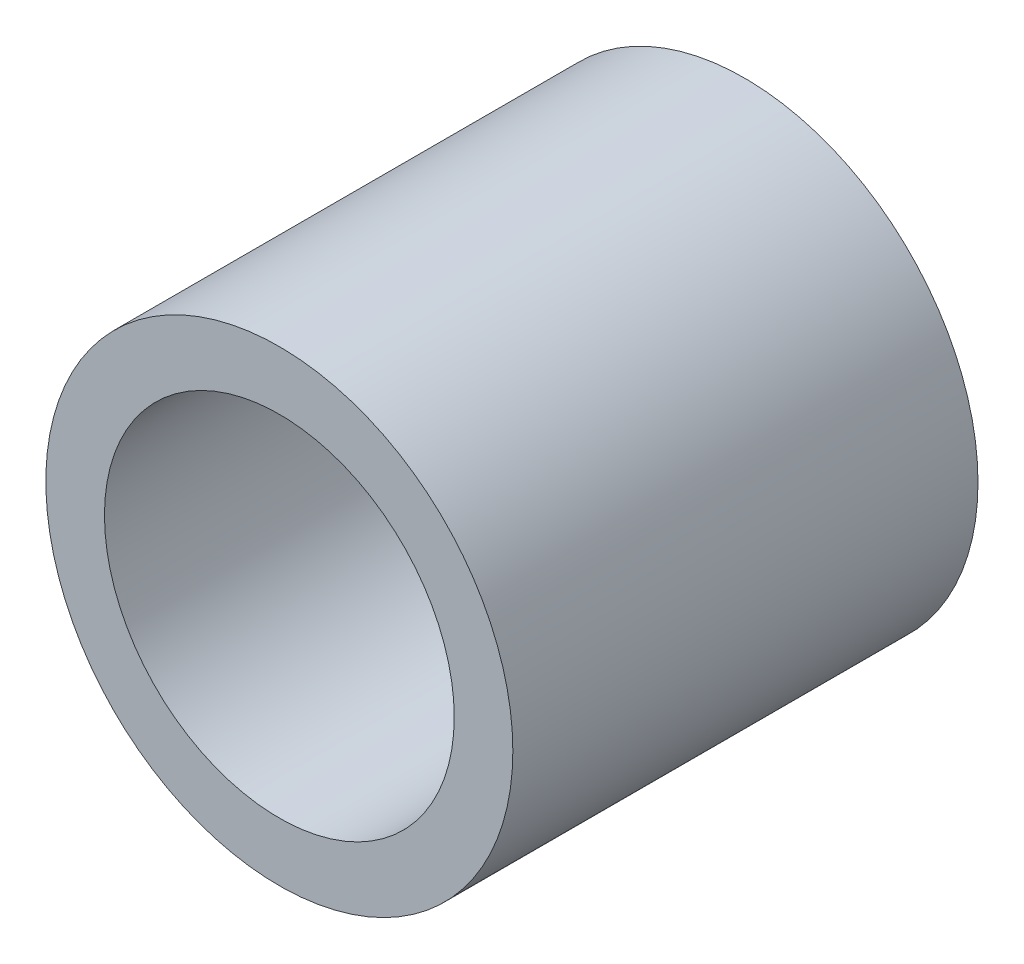
SolidWorks part; units mm, degrees
ref_plane "Front Plane" through (0, 0, 0) normal (0, 0, 1) x (1, 0, 0)
ref_plane "Top Plane" through (0, 0, 0) normal (0, 1, 0) x (1, 0, 0)
ref_plane "Right Plane" through (0, 0, 0) normal (1, 0, 0) x (0, 0, -1)
sketch "Sketch1" plane through (0, 0, 0) normal (0, 0, 1) x (1, 0, 0)
  circle A0 centre (0, 0) radius 6.3754
  circle A1 centre (0, 0) radius 4.7752
  dimension "D1" = 12.7508
  dimension "ID" = 9.5504
extrude "Extrude1" add sketch "Sketch1" along normal mid plane 12.7
sketch "Sketch2" plane through (0, 0, 0) normal (1, 0, 0) x (0, 0, -1)
  line L0 (-6.35, -4.7752) -> (6.35, -4.7752) construction
  line L3 (6.35, 4.7752) -> (-6.35, 4.7752) construction
  line L5 (-6.35, -4.7752) -> (6.35, -4.7752)
  line L6 (6.35, 4.7752) -> (-6.35, 4.7752)
sketch "Sketch4" plane through (0, 0, 6.35) normal (0, 0, 1) x (1, 0, 0)
  line L0 (0, 0) -> (-3.3766, 3.3766)
  line L1 (0, -3.4925) -> (0, 3.4925) construction
  circle A0 centre (0, 0) radius 4.7752 construction
  dimension "D1" = 45
